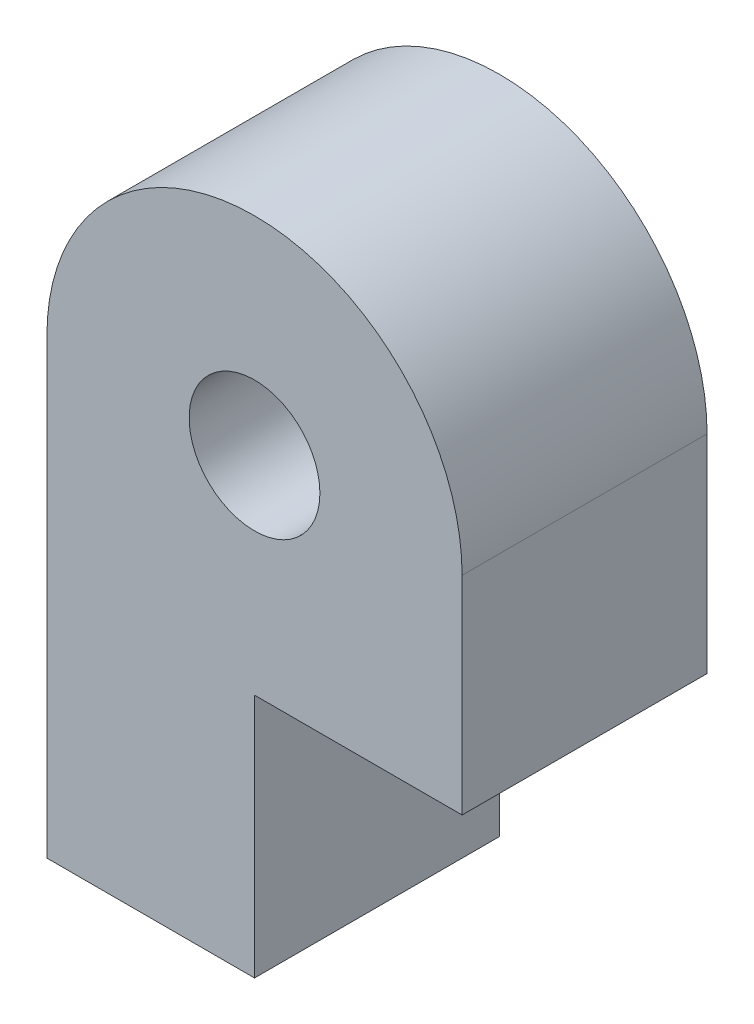
SolidWorks part; units mm, degrees
ref_plane "Front Plane" through (0, 0, 0) normal (0, 0, 1) x (1, 0, 0)
ref_plane "Top Plane" through (0, 0, 0) normal (0, 1, 0) x (1, 0, 0)
ref_plane "Right Plane" through (0, 0, 0) normal (1, 0, 0) x (0, 0, -1)
sketch "Sketch1" plane through (0, 0, 0) normal (0, 0, 1) x (1, 0, 0)
  line L0 (-5.08, 0) -> (-5.08, -5.08)
  line L1 (5.08, 0) -> (5.08, -5.08)
  line L2 (5.08, -5.08) -> (0, -5.08)
  line L3 (-5.08, -5.08) -> (-5.08, -11.0744)
  line L4 (-5.08, -11.0744) -> (0, -11.0744)
  line L5 (0, -11.0744) -> (0, -5.08)
  circle A0 centre (0, 0) radius 1.6
  arc A1 (5.08, 0) -> (-5.08, 0) centre (0, 0) ccw
extrude "Boss-Extrude1" add sketch "Sketch1" along normal blind 5.9944
